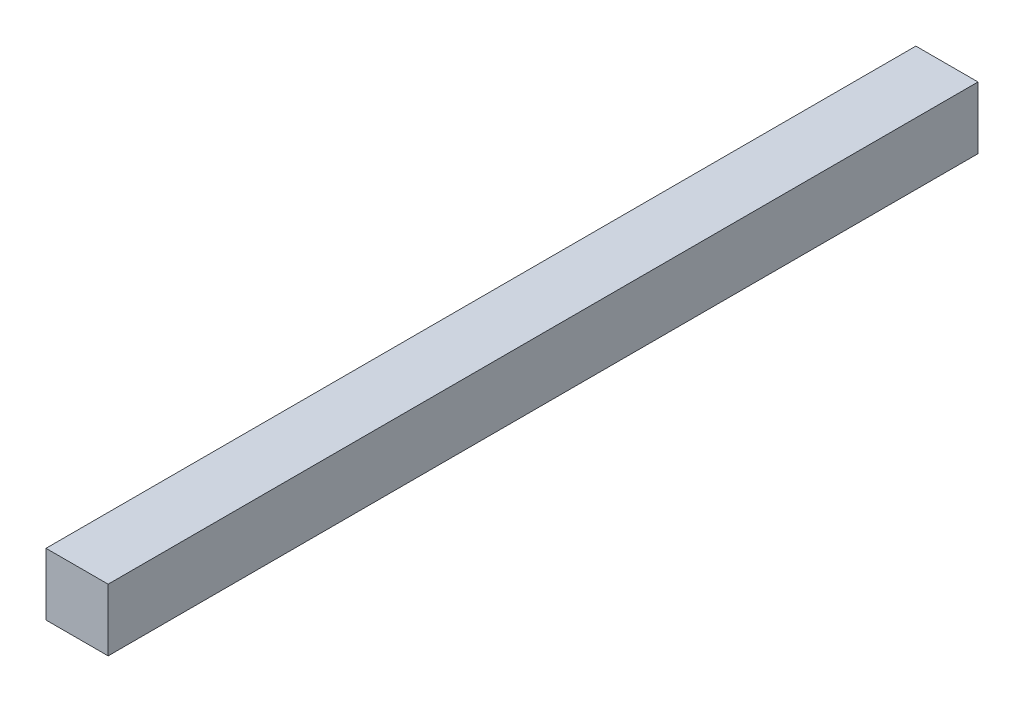
SolidWorks part; units mm, degrees
ref_plane "Front Plane" through (0, 0, 0) normal (0, 0, 1) x (1, 0, 0)
ref_plane "Top Plane" through (0, 0, 0) normal (0, 1, 0) x (1, 0, 0)
ref_plane "Right Plane" through (0, 0, 0) normal (1, 0, 0) x (0, 0, -1)
sketch "Sketch1" plane through (0, 0, 0) normal (0, 0, 1) x (1, 0, 0)
  line L1 (-104.4958, 34.1614) -> (-94.4958, 34.1614)
  line L2 (-104.4958, 34.1614) -> (-104.4958, 24.1614)
  line L3 (-104.4958, 24.1614) -> (-94.4958, 24.1614)
  line L4 (-94.4958, 34.1614) -> (-94.4958, 24.1614)
extrude "Boss-Extrude1" add sketch "Sketch1" along normal blind 140
